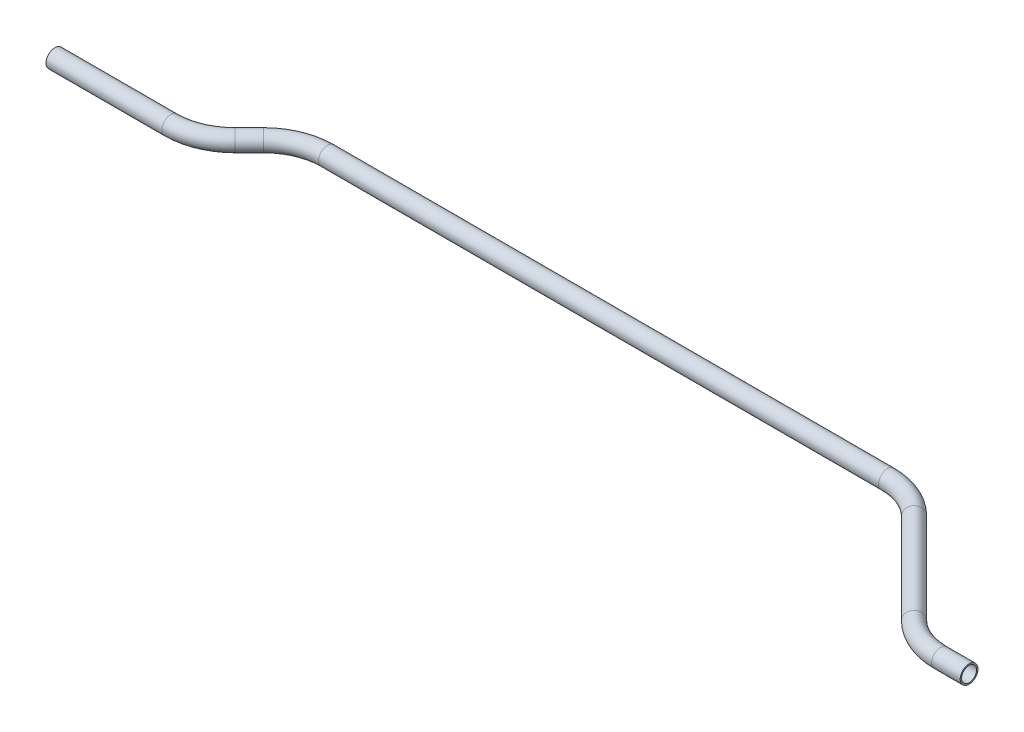
SolidWorks part; units mm, degrees
ref_plane "Front Plane" through (0, 0, 0) normal (0, 0, 1) x (1, 0, 0)
ref_plane "Top Plane" through (0, 0, 0) normal (0, 1, 0) x (1, 0, 0)
ref_plane "Right Plane" through (0, 0, 0) normal (1, 0, 0) x (0, 0, -1)
sketch "Sketch1" plane through (0, 0, 0) normal (0, 1, 0) x (1, 0, 0)
  line L0 (0, 0) -> (103.3277, 0)
  line L1 (143.7388, 16.7388) -> (156.405, 29.405)
  line L2 (196.8162, 46.1439) -> (696.0318, 46.1439)
  line L3 (736.4429, 29.405) -> (817.2652, -51.4173)
  line L4 (857.6764, -68.1561) -> (883.0764, -68.1561)
  arc A0 (817.2652, -51.4173) -> (857.6764, -68.1561) centre (857.6764, -11.0061) ccw
  arc A1 (696.0318, 46.1439) -> (736.4429, 29.405) centre (696.0318, -11.0061) cw
  arc A2 (156.405, 29.405) -> (196.8162, 46.1439) centre (196.8162, -11.0061) cw
  arc A3 (103.3277, 0) -> (143.7388, 16.7388) centre (103.3277, 57.15) ccw
  point P9 (834.0041, -68.1561)
  point P12 (719.7041, 46.1439)
  point P15 (173.1439, 46.1439)
  point P18 (127, 0)
  dimension "D8" = 57.15
  dimension "D1" = 127
  dimension "D2" = 135
  dimension "D3" = 25.4
  dimension "D4" = 883.0764
  dimension "D5" = 114.3
  dimension "D6" = 45
  dimension "D7" = 46.1439
ref_plane "Plane1" through (0, 0, 0) normal (1, 0, 0) x (0, 0, -1)
sketch "Sketch2" plane through (0, 0, 0) normal (1, 0, 0) x (0, 0, -1)
  circle A0 centre (0, 0) radius 7.9375
  circle A1 centre (0, 0) radius 6.6929
  dimension "D1" = 15.875
  dimension "D2" = 1.2446
sweep "Sweep1" add profiles "Sketch2" path "Sketch1"
